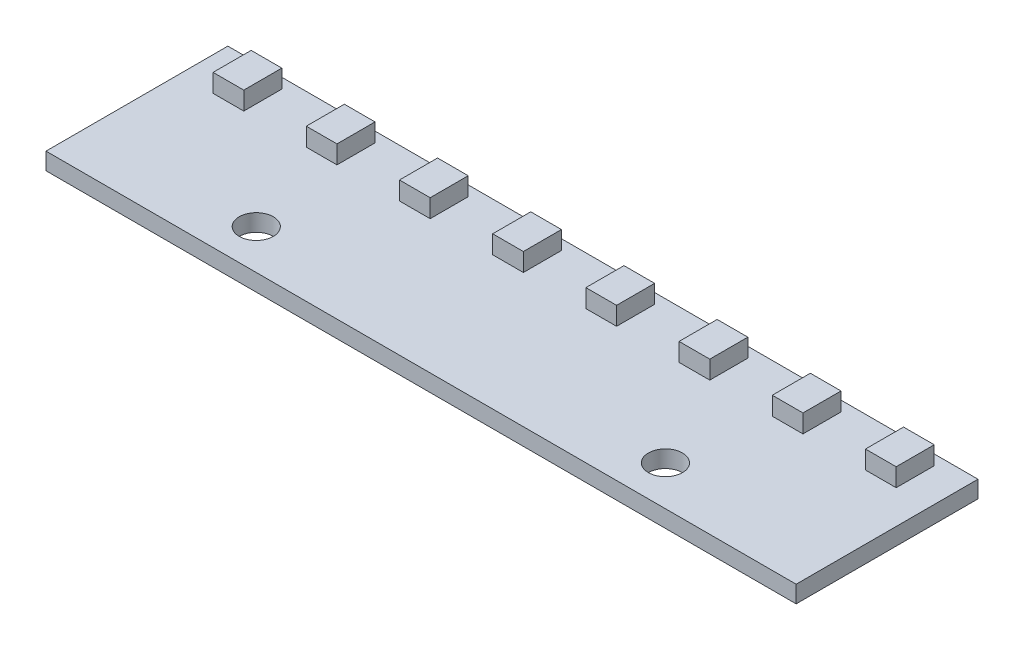
SolidWorks part; units mm, degrees
ref_plane "Front Plane" through (0, 0, 0) normal (0, 0, 1) x (1, 0, 0)
ref_plane "Top Plane" through (0, 0, 0) normal (0, 1, 0) x (1, 0, 0)
ref_plane "Right Plane" through (0, 0, 0) normal (1, 0, 0) x (0, 0, -1)
sketch "Sketch1" plane through (0, 0, 0) normal (0, 1, 0) x (1, 0, 0)
  line L0 (-18, -4.5) -> (18, -4.5) construction
  line L1 (-33, -8) -> (33, -8)
  line L2 (-33, -8) -> (-33, 8)
  line L3 (-33, 8) -> (33, 8)
  line L4 (33, -8) -> (33, 8)
  line L5 (-33, -8) -> (33, 8) construction
  line L6 (-33, 8) -> (33, -8) construction
  circle A0 centre (-18, -4.5) radius 1.5
  circle A1 centre (18, -4.5) radius 1.5
  point P0 (0, 0)
  point P10 (0, -4.5)
  dimension "D3" = 3
  dimension "D1" = 66
  dimension "D2" = 16
  dimension "D4" = 36
  dimension "D5" = 3.5
extrude "Boss-Extrude1" add sketch "Sketch1" against normal blind 1.5
sketch "Sketch4" plane through (0, 0, 0) normal (0, 1, 0) x (1, 0, 0)
  line L0 (33, 8) -> (-33, 8) construction
  line L1 (-5.45, 7.1) -> (-2.75, 7.1)
  line L2 (-5.45, 7.1) -> (-5.45, 3.75)
  line L3 (-5.45, 3.75) -> (-2.75, 3.75)
  line L4 (-2.75, 7.1) -> (-2.75, 3.75)
  line L5 (2.75, 7.1) -> (5.45, 7.1)
  line L6 (2.75, 7.1) -> (2.75, 3.75)
  line L7 (2.75, 3.75) -> (5.45, 3.75)
  line L8 (5.45, 7.1) -> (5.45, 3.75)
  line L9 (10.95, 7.1) -> (13.65, 7.1)
  line L10 (10.95, 7.1) -> (10.95, 3.75)
  line L11 (10.95, 3.75) -> (13.65, 3.75)
  line L12 (13.65, 7.1) -> (13.65, 3.75)
  line L13 (19.15, 7.1) -> (21.85, 7.1)
  line L14 (19.15, 7.1) -> (19.15, 3.75)
  line L15 (19.15, 3.75) -> (21.85, 3.75)
  line L16 (21.85, 7.1) -> (21.85, 3.75)
  line L17 (27.35, 7.1) -> (30.05, 7.1)
  line L18 (27.35, 7.1) -> (27.35, 3.75)
  line L19 (27.35, 3.75) -> (30.05, 3.75)
  line L20 (30.05, 7.1) -> (30.05, 3.75)
  line L21 (-13.65, 7.1) -> (-10.95, 7.1)
  line L22 (-13.65, 7.1) -> (-13.65, 3.75)
  line L23 (-13.65, 3.75) -> (-10.95, 3.75)
  line L24 (-10.95, 7.1) -> (-10.95, 3.75)
  line L25 (-30.05, 7.1) -> (-27.35, 7.1)
  line L26 (-30.05, 7.1) -> (-30.05, 3.75)
  line L27 (-30.05, 3.75) -> (-27.35, 3.75)
  line L28 (-27.35, 7.1) -> (-27.35, 3.75)
  line L29 (-21.85, 3.75) -> (-19.15, 3.75)
  line L30 (-21.85, 3.75) -> (-21.85, 7.1)
  line L31 (-21.85, 7.1) -> (-19.15, 7.1)
  line L32 (-19.15, 3.75) -> (-19.15, 7.1)
  dimension "D1" = 2.7
  dimension "D2" = 5.5
  dimension "D3" = 5.5
  dimension "D4" = 3.35
  dimension "D5" = 5.5
  dimension "D6" = 5.5
  dimension "D7" = 5.5
  dimension "D8" = 5.5
  dimension "D9" = 5.5
  dimension "D10" = 2.75
  dimension "D11" = 0.9
extrude "Boss-Extrude4" add sketch "Sketch4" along normal blind 1.6
ref_plane "Plane1" through (0, 0, -5.425) normal (0, 0, 1) x (1, 0, 0)
